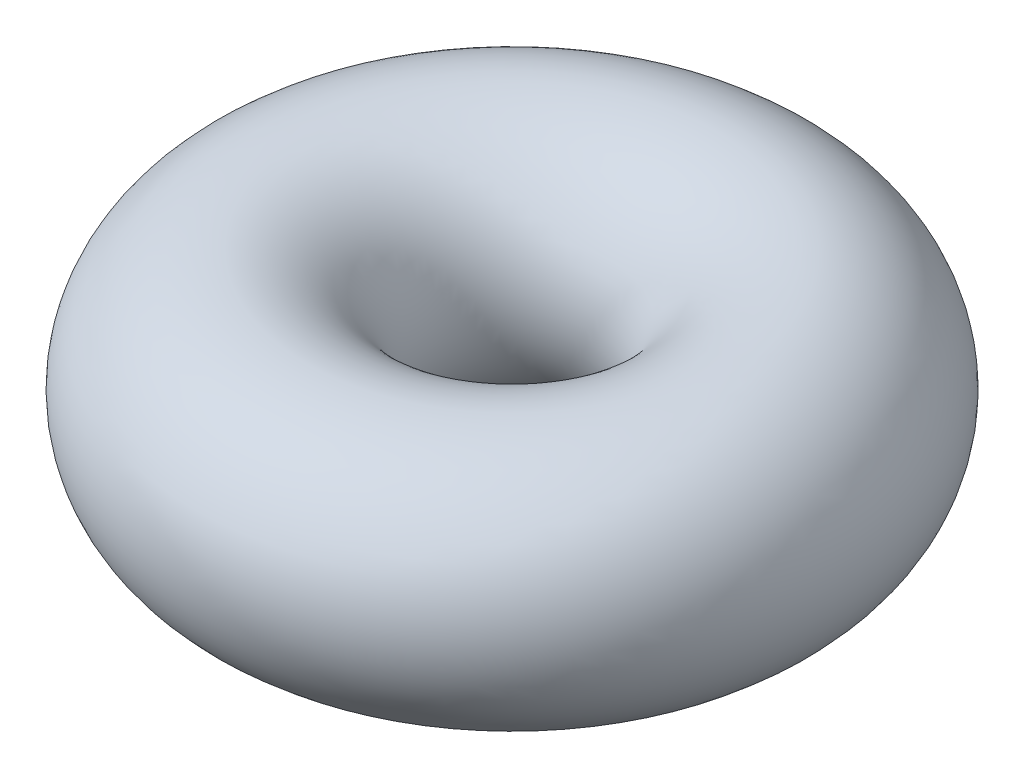
SolidWorks part; units mm, degrees
ref_plane "Front" through (0, 0, 0) normal (0, 0, 1) x (1, 0, 0)
ref_plane "Top" through (0, 0, 0) normal (0, 1, 0) x (1, 0, 0)
ref_plane "Right" through (0, 0, 0) normal (1, 0, 0) x (0, 0, -1)
sketch "Sketch1" plane through (0, 0, 0) normal (0, 0, 1) x (1, 0, 0)
  line L0 (0, 0) -> (0, -17.6937) construction
  line L1 (0, 0) -> (-4, 0) construction
  circle A0 centre (-4, 0) radius 2.375
  dimension "D2" = 4.75
  dimension "D1" = 4
revolve "Revolve1" add sketch "Sketch1" angle 360 about L0
sketch "Sketch2" plane through (0, 0, 0) normal (1, 0, 0) x (0, 0, -1)
  point P0 (0, 0)
